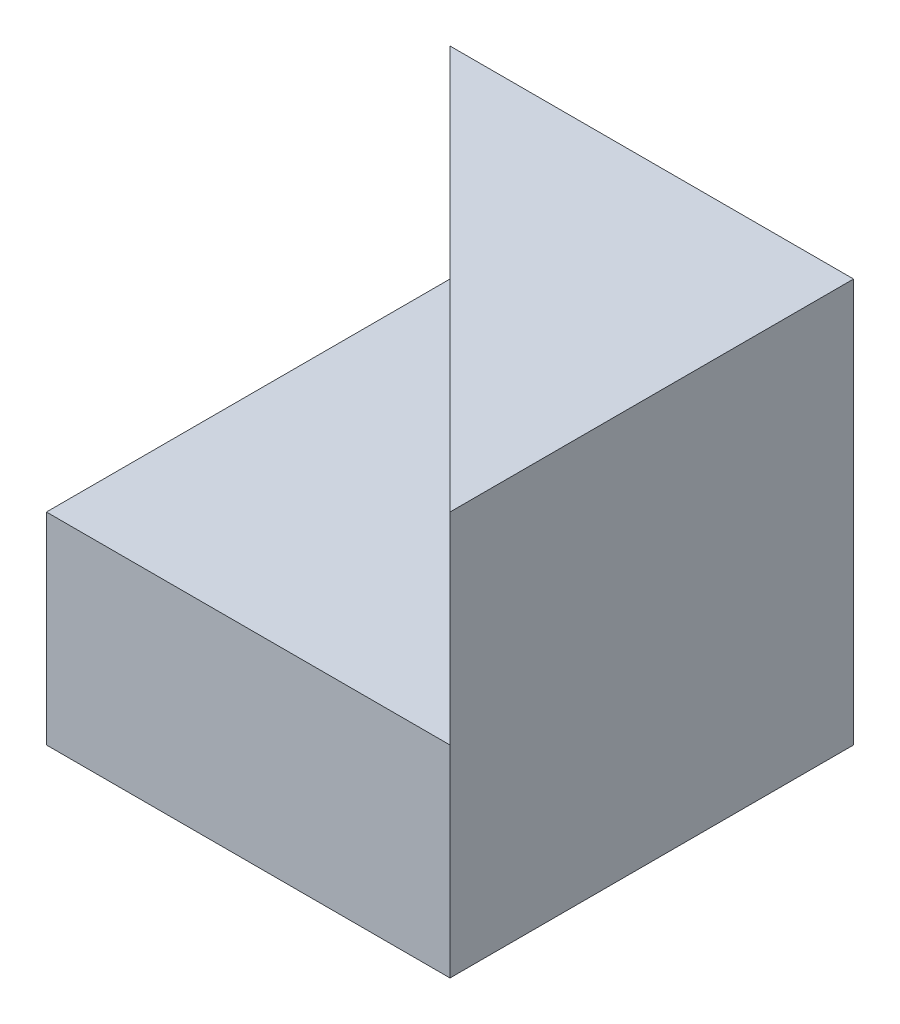
SolidWorks part; units mm, degrees
ref_plane "Front Plane" through (0, 0, 0) normal (0, 0, 1) x (1, 0, 0)
ref_plane "Top Plane" through (0, 0, 0) normal (0, 1, 0) x (1, 0, 0)
ref_plane "Right Plane" through (0, 0, 0) normal (1, 0, 0) x (0, 0, -1)
sketch "Sketch1" plane through (0, 0, 0) normal (0, 0, 1) x (1, 0, 0)
  line L1 (0, 0) -> (40, 0)
  line L2 (0, 0) -> (0, 40)
  line L3 (0, 40) -> (40, 40)
  line L4 (40, 0) -> (40, 40)
  dimension "D1" = 40
  dimension "D2" = 40
extrude "Boss-Extrude1" add sketch "Sketch1" along normal blind 40
sketch "Sketch4" plane through (0, 40, 0) normal (0, 1, 0) x (1, 0, 0)
  line L0 (0, 0) -> (40, -40)
  line L1 (40, -40) -> (0, -40)
  line L2 (0, -40) -> (0, 0)
extrude "Cut-Extrude2" cut sketch "Sketch4" against normal blind 20
